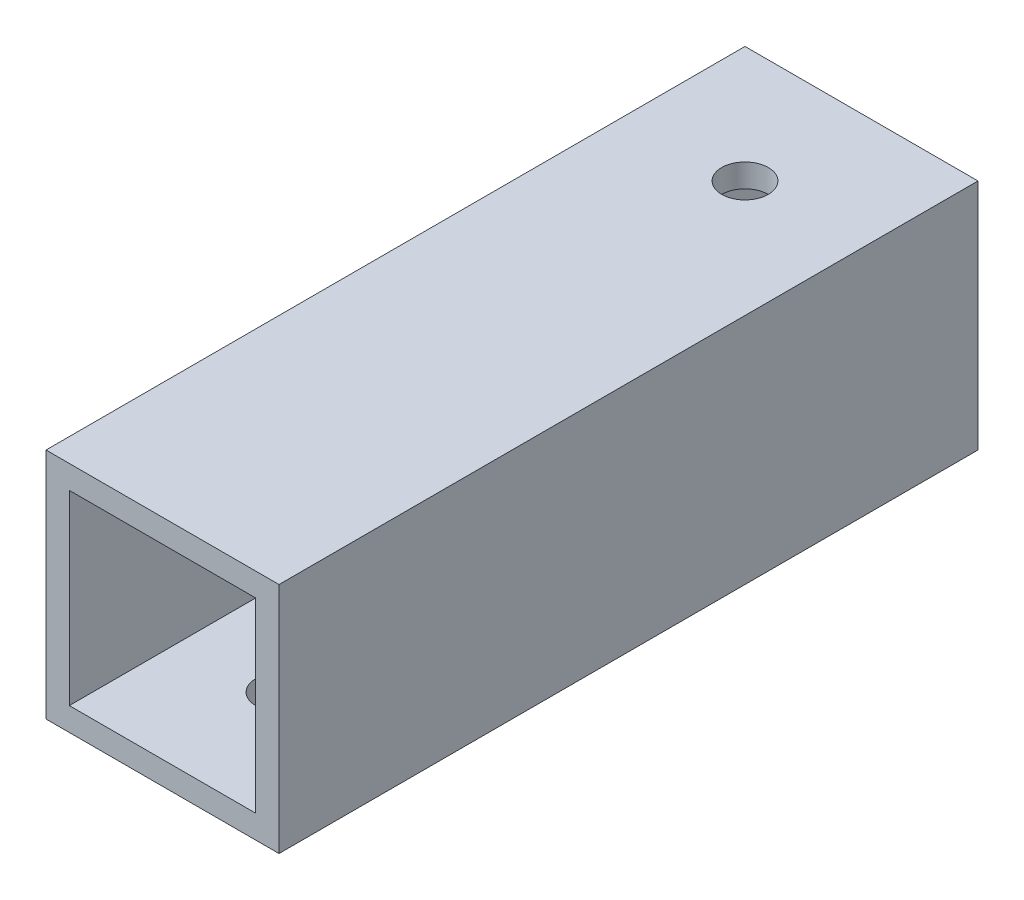
SolidWorks part; units mm, degrees
material "1060 合金"
ref_plane "正面" through (0, 0, 0) normal (0, 0, 1) x (1, 0, 0)
ref_plane "平面" through (0, 0, 0) normal (0, 1, 0) x (1, 0, 0)
ref_plane "右側面" through (0, 0, 0) normal (1, 0, 0) x (0, 0, -1)
sketch "ｽｹｯﾁ1" plane through (0, 0, 0) normal (0, 0, 1) x (1, 0, 0)
  line L1 (-7.0101, 7.7326) -> (7.9899, 7.7326)
  line L2 (-7.0101, 7.7326) -> (-7.0101, -7.2674)
  line L3 (-7.0101, -7.2674) -> (7.9899, -7.2674)
  line L4 (7.9899, 7.7326) -> (7.9899, -7.2674)
  line L9 (-5.5101, 6.2326) -> (6.4899, 6.2326)
  line L10 (-5.5101, 6.2326) -> (-5.5101, -5.7674)
  line L11 (-5.5101, -5.7674) -> (6.4899, -5.7674)
  line L12 (6.4899, 6.2326) -> (6.4899, -5.7674)
  dimension "D1" = 15
  dimension "D2" = 15
  dimension "D3" = 1.5
  dimension "D4" = 1.5
  dimension "D5" = 12
  dimension "D6" = 12
extrude "ﾎﾞｽ - 押し出し2" add sketch "ｽｹｯﾁ1" along normal blind 45
sketch "ｽｹｯﾁ2" plane through (0, 7.7326, 0) normal (0, 1, 0) x (1, 0, 0)
  line L0 (7.9899, 0) -> (-7.0101, 0) construction
  line L1 (7.9899, -45) -> (7.9899, 0) construction
  circle A0 centre (0.4899, -7.5) radius 1.5
  dimension "D1" = 7.5
  dimension "D2" = 7.5
extrude "ｶｯﾄ - 押し出し1" cut sketch "ｽｹｯﾁ2" against normal blind 10
sketch "ｽｹｯﾁ3" plane through (0, -7.2674, 0) normal (0, -1, 0) x (1, 0, 0)
  line L0 (-7.0101, 45) -> (7.9899, 45) construction
  line L1 (7.9899, 45) -> (7.9899, 0) construction
  circle A0 centre (0.4899, 37.5) radius 1.5
  dimension "D1" = 7.5
  dimension "D2" = 7.5
extrude "ｶｯﾄ - 押し出し2" cut sketch "ｽｹｯﾁ3" against normal blind 10
sketch "ｽｹｯﾁ7" plane through (-7.0101, 0, 0) normal (-1, 0, 0) x (0, 0, 1)
  line L0 (45, -7.2674) -> (0, -7.2674) construction
  line L1 (45, 7.7326) -> (45, -7.2674) construction
  circle A0 centre (25.6, -2.9674) radius 1
  circle A1 centre (14.8, -2.9674) radius 1
  dimension "D1" = 4.3
  dimension "D2" = 4.3
  dimension "D3" = 10.8
  dimension "D4" = 19.4
extrude "ｶｯﾄ - 押し出し5" cut sketch "ｽｹｯﾁ7" against normal blind 10
